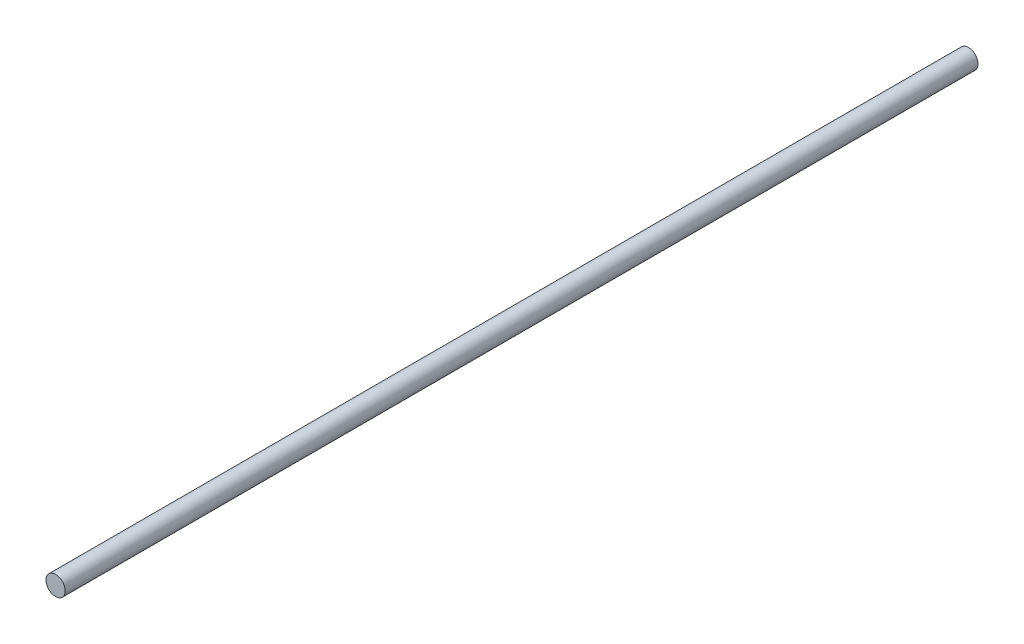
SolidWorks part; units mm, degrees
ref_plane "Front Plane" through (0, 0, 0) normal (0, 0, 1) x (1, 0, 0)
ref_plane "Top Plane" through (0, 0, 0) normal (0, 1, 0) x (1, 0, 0)
ref_plane "Right Plane" through (0, 0, 0) normal (1, 0, 0) x (0, 0, -1)
sketch "Sketch1" plane through (0, 0, 0) normal (0, 0, 1) x (1, 0, 0)
  circle A0 centre (0, 0) radius 3
  dimension "D1" = 6
extrude "Boss-Extrude1" add sketch "Sketch1" along normal blind 285
